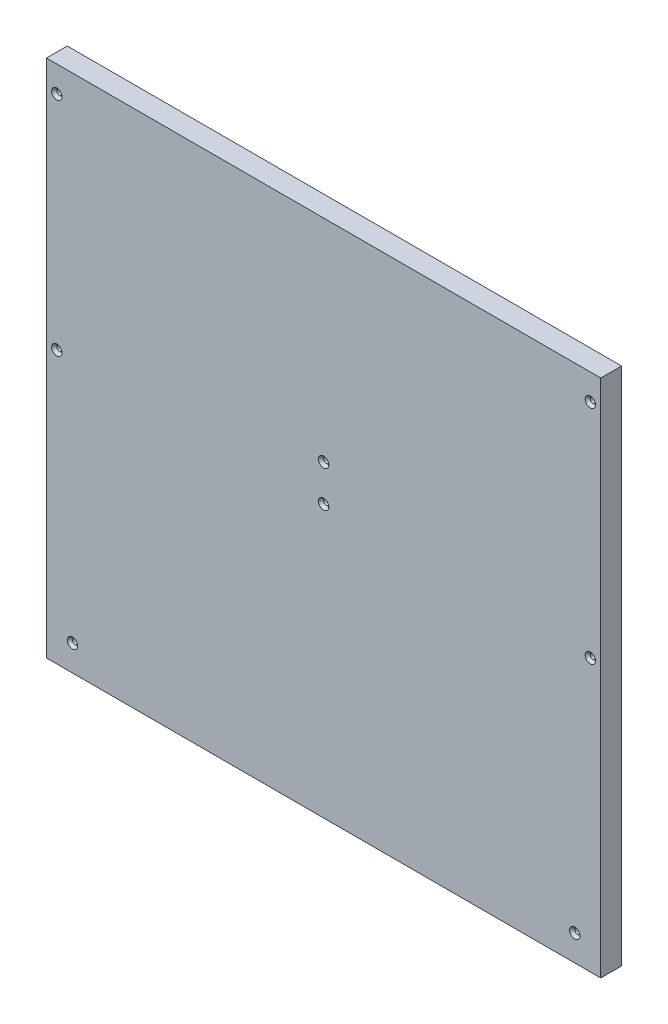
SolidWorks part; units mm, degrees
ref_plane "Front Plane" through (0, 0, 0) normal (0, 0, 1) x (1, 0, 0)
ref_plane "Top Plane" through (0, 0, 0) normal (0, 1, 0) x (1, 0, 0)
ref_plane "Right Plane" through (0, 0, 0) normal (1, 0, 0) x (0, 0, -1)
sketch "Sketch1" plane through (0, 0, 0) normal (0, 0, 1) x (1, 0, 0)
  line L0 (168.5078, 240.7254) -> (168.5078, -59.2746) construction
  line L1 (-145.4922, 240.7254) -> (174.5078, 240.7254)
  line L2 (-145.4922, 240.7254) -> (-145.4922, -59.2746)
  line L3 (-145.4922, -59.2746) -> (174.5078, -59.2746)
  line L4 (174.5078, 240.7254) -> (174.5078, -59.2746)
  line L5 (-139.4922, 240.7254) -> (-139.4922, -59.2746) construction
  line L6 (14.5078, -59.2746) -> (14.5078, 240.7254) construction
  circle A0 centre (-139.4922, 225.7254) radius 1.5
  circle A1 centre (-139.4922, 97.7254) radius 1.5
  circle A2 centre (168.5078, 225.7254) radius 1.5
  circle A3 centre (168.5078, 97.7254) radius 1.5
  circle A4 centre (-130.4922, -44.2746) radius 1.5
  circle A5 centre (159.5078, -44.2746) radius 1.5
  circle A6 centre (14.5078, 97.7254) radius 1.5
  circle A7 centre (14.5078, 118.7254) radius 1.5
  dimension "D7" = 3
  dimension "D8" = 3
  dimension "D9" = 3
  dimension "D10" = 3
  dimension "D13" = 3
  dimension "D14" = 3
  dimension "D15" = 3
  dimension "D22" = 3
  dimension "D1" = 320
  dimension "D2" = 300
  dimension "D3" = 6
  dimension "D4" = 6
  dimension "D5" = 15
  dimension "D6" = 15
  dimension "D11" = 143
  dimension "D12" = 143
  dimension "D16" = 15
  dimension "D17" = 15
  dimension "D18" = 15
  dimension "D19" = 15
  dimension "D20" = 157
  dimension "D21" = 160
  dimension "D23" = 122
extrude "Boss-Extrude1" add sketch "Sketch1" along normal blind 12
sketch "Sketch2" plane through (0, 0, 0) normal (0, 0, 1) x (1, 0, 0)
  circle A0 centre (-139.4922, 225.7254) radius 3
  circle A1 centre (-139.4922, 97.7254) radius 3
  circle A2 centre (168.5078, 225.7254) radius 3
  circle A3 centre (168.5078, 97.7254) radius 3
  circle A4 centre (14.5078, 97.7254) radius 3
  circle A5 centre (159.5078, -44.2746) radius 3
  circle A6 centre (-130.4922, -44.2746) radius 3
  circle A7 centre (14.5078, 118.7254) radius 3
  dimension "D1" = 6
  dimension "D2" = 6
  dimension "D3" = 6
  dimension "D4" = 6
  dimension "D5" = 6
  dimension "D6" = 6
  dimension "D7" = 6
  dimension "D8" = 6
extrude "Cut-Extrude1" cut sketch "Sketch2" against normal blind 3 draft 45 from surface at 12
